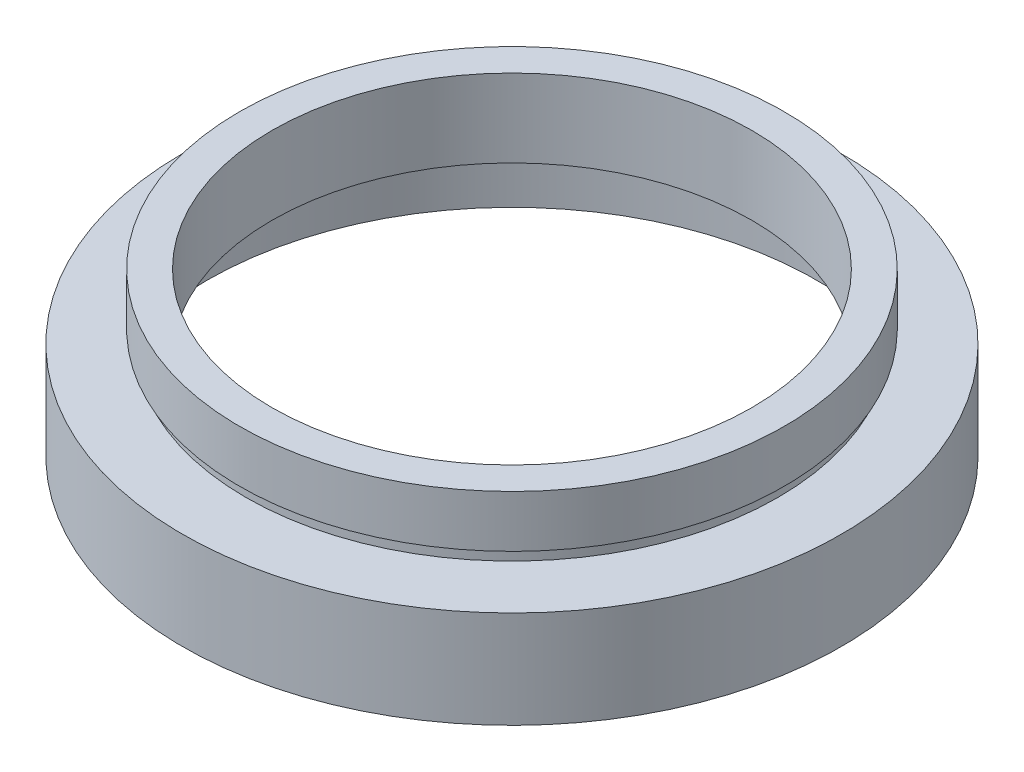
SolidWorks part; units mm, degrees
ref_plane "前视基准面" through (0, 0, 0) normal (0, 0, 1) x (1, 0, 0)
ref_plane "上视基准面" through (0, 0, 0) normal (0, 1, 0) x (1, 0, 0)
ref_plane "右视基准面" through (0, 0, 0) normal (1, 0, 0) x (0, 0, -1)
sketch "草图1" plane through (0, 0, 0) normal (0, 0, 1) x (1, 0, 0)
  line L0 (0, 16.886) -> (0, -24.4878) construction
  line L1 (23.5, 0) -> (23.5, 5.5)
  line L2 (18.5, 6.5) -> (24.1, 6.5)
  line L3 (18.5, 6.5) -> (18.5, 12.5)
  line L4 (18.5, 12.5) -> (21, 12.5)
  line L5 (21, 12.5) -> (21, 8.5)
  line L6 (21, 8.5) -> (20.5, 8.5)
  line L7 (20.5, 8.5) -> (20.5, 7.5)
  line L8 (20.5, 7.5) -> (25.4, 7.5)
  line L9 (25.4, 7.5) -> (25.4, 0)
  line L10 (25.4, 0) -> (23.5, 0)
  line L11 (23.5, 5.5) -> (24.1, 5.5)
  line L12 (24.1, 5.5) -> (24.1, 6.5)
  line L13 (0, 0) -> (3.4668, 0) construction
  point P4 (24.45, 0)
  dimension "D1" = 18.5
  dimension "D2" = 21
  dimension "D3" = 20.5
  dimension "D4" = 23.5
  dimension "D5" = 24.1
  dimension "D6" = 25.4
  dimension "D7" = 12.5
  dimension "D8" = 7.5
  dimension "D9" = 1
  dimension "D10" = 5.5
  dimension "D11" = 1
revolve "旋转1" add sketch "草图1" angle 360 about L0
cosmetic thread "装饰螺纹线1"
cosmetic thread "装饰螺纹线2"
cosmetic thread "装饰螺纹线3"
